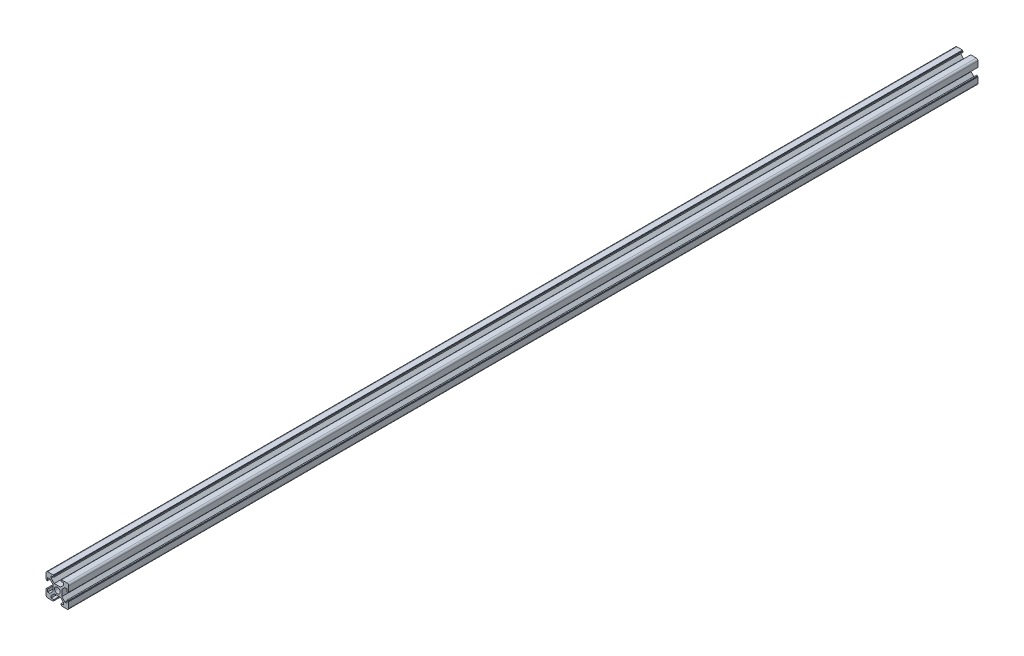
SolidWorks part; units mm, degrees
ref_plane "前视基准面" through (0, 0, 0) normal (0, 0, 1) x (1, 0, 0)
ref_plane "上视基准面" through (0, 0, 0) normal (0, 1, 0) x (1, 0, 0)
ref_plane "右视基准面" through (0, 0, 0) normal (1, 0, 0) x (0, 0, -1)
sketch "草图1" plane through (0, 0, 0) normal (0, 0, 1) x (1, 0, 0)
  line L0 (-3.6, 10) -> (-3.6, 9.5)
  line L1 (-3.6, 9.5) -> (-3.1, 9.5)
  line L2 (-3.1, 9.5) -> (-3.1, 8.5)
  line L3 (-3.1, 8.5) -> (-5.5, 8.5)
  line L4 (-8.5, -10) -> (-3.6, -10)
  line L5 (-10, -8.5) -> (-10, -3.6)
  line L6 (8.5, 10) -> (3.6, 10)
  line L7 (10, 8.5) -> (10, 3.6)
  line L8 (0, 14.8756) -> (0, 0) construction
  line L9 (0, 0) -> (14.1675, 0) construction
  line L10 (-5.5, 8.5) -> (-5.5, 6.65)
  line L11 (-5.5, 6.65) -> (-2.75, 3.9)
  line L12 (-2.75, 3.9) -> (2.75, 3.9)
  line L13 (5.5, 6.65) -> (2.75, 3.9)
  line L14 (5.5, 8.5) -> (5.5, 6.65)
  line L15 (3.1, 8.5) -> (5.5, 8.5)
  line L16 (3.1, 9.5) -> (3.1, 8.5)
  line L17 (3.6, 9.5) -> (3.1, 9.5)
  line L18 (3.6, 10) -> (3.6, 9.5)
  line L19 (-3.6, 10) -> (-8.5, 10)
  line L20 (10, 3.6) -> (9.5, 3.6)
  line L21 (9.5, 3.6) -> (9.5, 3.1)
  line L22 (9.5, 3.1) -> (8.5, 3.1)
  line L23 (8.5, 3.1) -> (8.5, 5.5)
  line L24 (8.5, 5.5) -> (6.65, 5.5)
  line L25 (6.65, 5.5) -> (3.9, 2.75)
  line L26 (3.9, 2.75) -> (3.9, -2.75)
  line L27 (6.65, -5.5) -> (3.9, -2.75)
  line L28 (8.5, -5.5) -> (6.65, -5.5)
  line L29 (8.5, -3.1) -> (8.5, -5.5)
  line L30 (9.5, -3.1) -> (8.5, -3.1)
  line L31 (9.5, -3.6) -> (9.5, -3.1)
  line L32 (10, -3.6) -> (9.5, -3.6)
  line L33 (3.6, -10) -> (3.6, -9.5)
  line L34 (3.6, -9.5) -> (3.1, -9.5)
  line L35 (3.1, -9.5) -> (3.1, -8.5)
  line L36 (3.1, -8.5) -> (5.5, -8.5)
  line L37 (5.5, -8.5) -> (5.5, -6.65)
  line L38 (5.5, -6.65) -> (2.75, -3.9)
  line L39 (2.75, -3.9) -> (-2.75, -3.9)
  line L40 (-5.5, -6.65) -> (-2.75, -3.9)
  line L41 (-5.5, -8.5) -> (-5.5, -6.65)
  line L42 (-3.1, -8.5) -> (-5.5, -8.5)
  line L43 (-3.1, -9.5) -> (-3.1, -8.5)
  line L44 (-3.6, -9.5) -> (-3.1, -9.5)
  line L45 (-3.6, -10) -> (-3.6, -9.5)
  line L46 (-10, -3.6) -> (-9.5, -3.6)
  line L47 (-9.5, -3.6) -> (-9.5, -3.1)
  line L48 (-9.5, -3.1) -> (-8.5, -3.1)
  line L49 (-8.5, -3.1) -> (-8.5, -5.5)
  line L50 (-8.5, -5.5) -> (-6.65, -5.5)
  line L51 (-6.65, -5.5) -> (-3.9, -2.75)
  line L52 (-3.9, -2.75) -> (-3.9, 2.75)
  line L53 (-6.65, 5.5) -> (-3.9, 2.75)
  line L54 (-8.5, 5.5) -> (-6.65, 5.5)
  line L55 (-8.5, 3.1) -> (-8.5, 5.5)
  line L56 (-9.5, 3.1) -> (-8.5, 3.1)
  line L57 (-9.5, 3.6) -> (-9.5, 3.1)
  line L58 (-10, 3.6) -> (-9.5, 3.6)
  line L59 (3.6, -10) -> (8.5, -10)
  line L60 (-10, 3.6) -> (-10, 8.5)
  line L61 (10, -3.6) -> (10, -8.5)
  circle A0 centre (0, 0) radius 2.5
  arc A1 (-10, 8.5) -> (-8.5, 10) centre (-8.5, 8.5) cw
  arc A2 (10, 8.5) -> (8.5, 10) centre (8.5, 8.5) ccw
  arc A3 (-8.5, -10) -> (-10, -8.5) centre (-8.5, -8.5) cw
  arc A4 (8.5, -10) -> (10, -8.5) centre (8.5, -8.5) ccw
  point P0 (-10, 0)
  point P1 (10, 0)
  point P2 (0, 10)
  point P3 (0, -10)
  point P4 (0, 0)
  point P5 (-10, -10)
  point P6 (10, -10)
  point P7 (10, 10)
  point P8 (-10, 10)
  point P13 (0, 0)
  dimension "D1" = 11
  dimension "D2" = 20
  dimension "D3" = 6.2
  dimension "D4" = 7.2
  dimension "D5" = 6.1
  dimension "D6" = 5
  dimension "D7" = 1.5
  dimension "D8" = 45
  dimension "D9" = 0.5
  dimension "D10" = 1
  dimension "D11" = 5.5
extrude "凸台-拉伸1" add sketch "草图1" along normal blind 800
